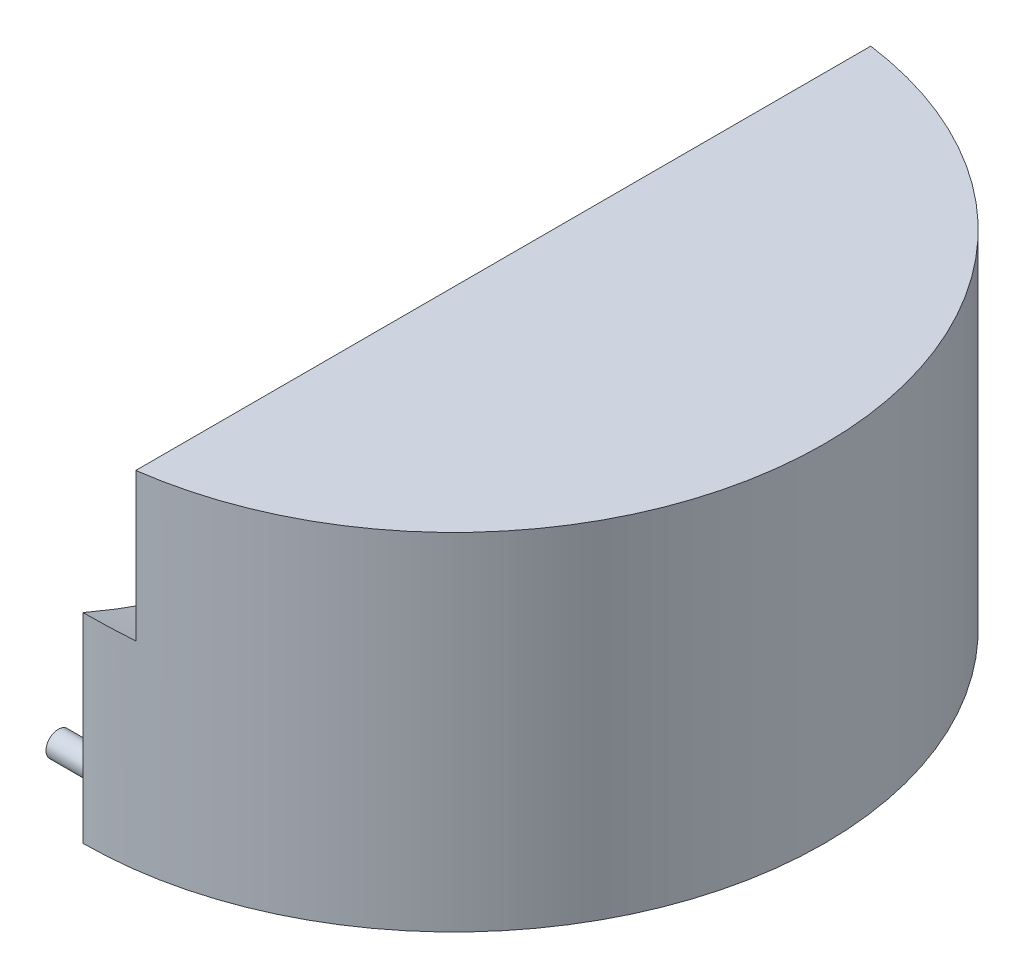
SolidWorks part; units mm, degrees
ref_plane "Front Plane" through (0, 0, 0) normal (0, 0, 1) x (1, 0, 0)
ref_plane "Top Plane" through (0, 0, 0) normal (0, 1, 0) x (1, 0, 0)
ref_plane "Right Plane" through (0, 0, 0) normal (1, 0, 0) x (0, 0, -1)
sketch "Sketch1" plane through (0, 0, 0) normal (0, 1, 0) x (1, 0, 0)
  line L0 (0, 75) -> (0, -75)
  circle A0 centre (0, 0) radius 75
  dimension "D1" = 150
extrude "Boss-Extrude2" add sketch "Sketch1" along normal blind 100 contours L0 A0
sketch "Sketch3" plane through (0, 0, 0) normal (0, -1, 0) x (-1, 0, 0)
  line L0 (0, 0) -> (-75, 0) construction
  line L2 (-54, 0) -> (-65, 0)
  line L3 (-54, 0) -> (-54, 22)
  line L4 (-54, 22) -> (-65, 22)
  line L5 (-65, 0) -> (-65, 22)
  arc A0 (0, 75) -> (0, -75) centre (0, 0) ccw construction
  dimension "D1" = 10
  dimension "D2" = 11
  dimension "D3" = 22
revolve "Cut-Revolve3" cut sketch "Sketch3" angle 360 about L0
sketch "Sketch4" plane through (65, 0, 0) normal (-1, 0, 0) x (0, 0, 1)
  line L0 (22, 0) -> (-22, 0) construction
  circle A0 centre (0, 0) radius 1
  dimension "D1" = 2
extrude "Cut-Extrude1" cut sketch "Sketch4" against normal blind 2
sketch "Sketch5" plane through (54, 0, 0) normal (1, 0, 0) x (0, 0, -1)
  line L0 (22, 0) -> (-22, 0) construction
  circle A0 centre (0, 0) radius 1
  dimension "D1" = 2
extrude "Cut-Extrude2" cut sketch "Sketch5" against normal blind 2
pattern_circular "CirPattern1" count 4 every 90 about axis through (0, 0, 0) along (0, 1, 0) of "Cut-Revolve3", "Cut-Extrude1", "Cut-Extrude2"
sketch "Sketch6" plane through (0, 100, 0) normal (0, 1, 0) x (1, 0, 0)
  line L0 (0, 75) -> (0, -75) construction
  line L1 (0, 0) -> (10, 0)
  line L2 (0, 0) -> (0, -190)
  line L3 (0, -190) -> (10, -190)
  line L4 (10, 0) -> (10, -190)
  dimension "D1" = 10
  dimension "D2" = 190
sketch "Sketch8" plane through (0, 0, 0) normal (-1, 0, 0) x (0, 0, 1)
  line L0 (-75, 0) -> (-67, 0) construction
  line L1 (-75, 50.2506) -> (-75, 0) construction
  line L2 (0, -1000) -> (0, 49000) construction
  line L3 (-52, 0) -> (52, 0) construction
  line L4 (-40, 5) -> (-20, 5)
  line L5 (-40, 5) -> (-40, 0)
  line L6 (-40, 0) -> (-20, 0)
  line L7 (-20, 5) -> (-20, 0)
  line L8 (40, 0) -> (20, 0)
  line L9 (20, 5) -> (20, 0)
  line L10 (40, 5) -> (20, 5)
  line L11 (40, 5) -> (40, 0)
  circle A0 centre (-70, 10) radius 2.5
  circle A1 centre (70, 10) radius 2.5
  dimension "D1" = 5
  dimension "D2" = 10
  dimension "D3" = 5
  dimension "D4" = 20
  dimension "D5" = 5
  dimension "D6" = 20
extrude "Boss-Extrude3" add sketch "Sketch8" along normal blind 10
extrude "Boss-Extrude4" add sketch "Sketch6" along normal blind 115
sketch "Sketch10" plane through (0, 215, 0) normal (0, 1, 0) x (1, 0, 0)
  line L1 (10, 0) -> (0, 0)
  line L2 (10, 0) -> (10, -190)
  line L3 (10, -190) -> (0, -190)
  line L4 (0, 0) -> (0, -190)
revolve "Cut-Revolve4" cut sketch "Sketch10" angle 360 about L1
sketch "Sketch11" plane through (10, 0, 0) normal (-1, 0, 0) x (0, 0, 1)
  line L0 (74.3303, 40.1429) -> (74.3303, 100) construction
  line L1 (-74.3303, 100) -> (74.3303, 100) construction
  circle A0 centre (-0.6697, 47.5) radius 1
  circle A1 centre (-65.6697, 60.5) radius 1
  circle A2 centre (64.3303, 60.5) radius 1
  arc A3 (-74.3303, 40.1429) -> (74.3303, 40.1429) centre (0, 215) ccw construction
  circle A4 centre (-0.6697, 228.3541) radius 200.0539 construction
  dimension "D3" = 2
  dimension "D7" = 2
  dimension "D8" = 2
  dimension "D1" = 75
  dimension "D2" = 52.5
  dimension "D4" = 167.5
  dimension "D5" = 180
  dimension "D6" = 180
  dimension "D9" = 65
  dimension "D10" = 13
  dimension "D11" = 65
  dimension "D12" = 13
extrude "Cut-Extrude3" cut sketch "Sketch11" against normal blind 2
sketch "Sketch12" plane through (0, 100, 0) normal (0, 1, 0) x (1, 0, 0)
  circle A0 centre (0, 0) radius 75
  dimension "D1" = 150
extrude "Cut-Extrude4" cut sketch "Sketch12" against normal blind 30
